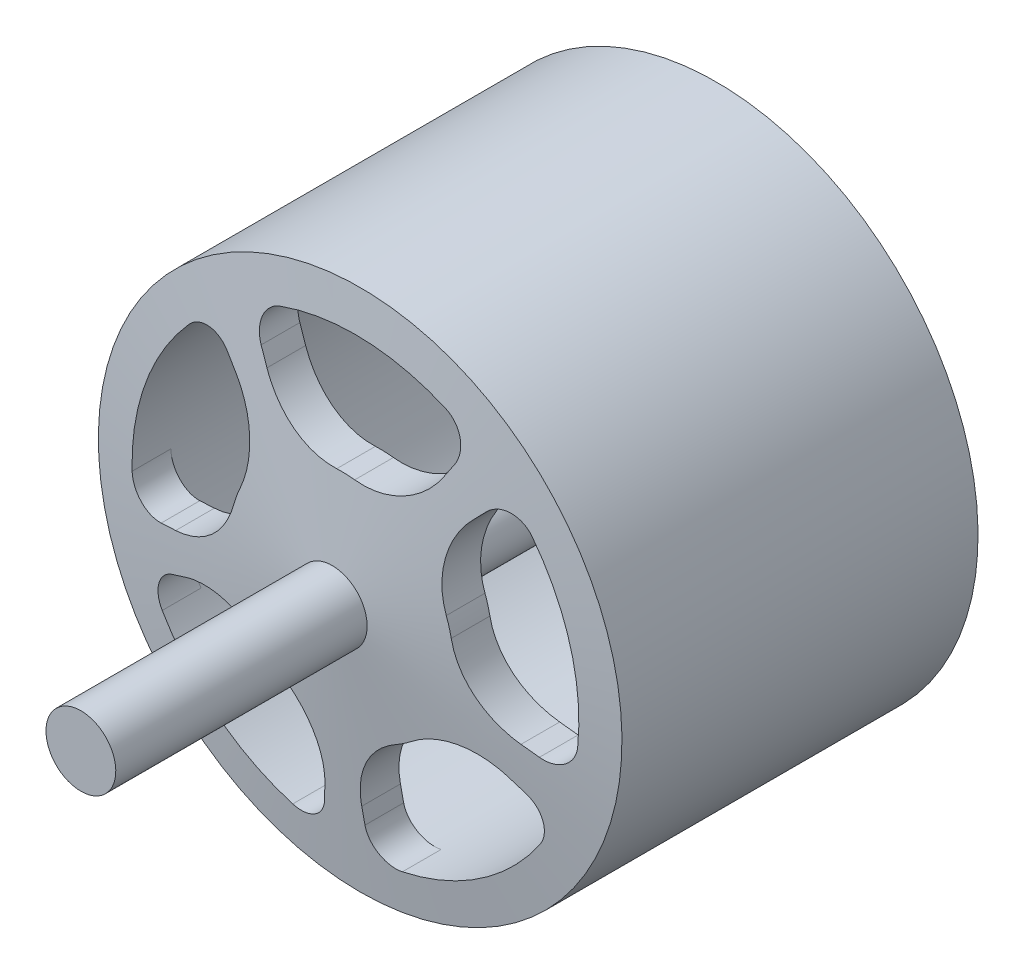
SolidWorks part; units mm, degrees
material "AISI 1020 Steel, Cold Rolled"
ref_plane "Front Plane" through (0, 0, 0) normal (0, 0, 1) x (1, 0, 0)
ref_plane "Top Plane" through (0, 0, 0) normal (0, 1, 0) x (1, 0, 0)
ref_plane "Right Plane" through (0, 0, 0) normal (1, 0, 0) x (0, 0, -1)
sketch "Sketch1" plane through (0, 0, 0) normal (1, 0, 0) x (0, 0, -1)
  line L0 (0, 0) -> (-45.5, 0) construction
  line L1 (-45.5, 0) -> (-45.5, 2.5)
  line L2 (-45.5, 2.5) -> (-27.5, 2.5)
  line L3 (-27.5, 2.5) -> (-25.5, 18.75)
  line L4 (-25.5, 18.75) -> (0, 18.75)
  line L5 (0, 18.75) -> (0, 0) construction
  line L6 (-45.5, 0) -> (0, 0)
  line L8 (-23.0677, 16) -> (0, 16)
  line L9 (0, 16) -> (0, 18.75)
  line L10 (-27.5, 2.5) -> (-24.7706, 2.1641) construction
  line L12 (7.7, 2.5) -> (-24.7292, 2.5)
  line L13 (-23.0677, 16) -> (-24.7706, 2.1641) construction
  line L14 (-23.0677, 16) -> (-24.7292, 2.5)
  line L15 (7.7, 2.5) -> (7.7, 0)
  line L16 (7.7, 0) -> (0, 0)
  dimension "D1" = 18.75
  dimension "D2" = 2.5
  dimension "D3" = 18
  dimension "D4" = 45.5
  dimension "D5" = 20
  dimension "D6" = 16
  dimension "D7" = 53.2
revolve "Revolve1" add sketch "Sketch1" angle 360 about L6
sketch "Sketch2" plane through (0, 0, 0) normal (0, 0, 1) x (1, 0, 0)
  line L0 (0, 0) -> (8.497, 13.5573) construction
  line L1 (0, 0) -> (-7.4924, 14.1373) construction
  line L2 (-6.4886, 12.2433) -> (-5.9233, 11.1765)
  line L3 (7.3587, 11.741) -> (6.7175, 10.718)
  circle A0 centre (0, 0) radius 16 construction
  arc A1 (-5.396, 15.0627) -> (6.4731, 14.6321) centre (0, 0) cw
  circle A2 centre (0, 0) radius 8 construction
  arc A3 (-0.3553, 7.9921) -> (0.9334, 7.9454) centre (0, 0) cw
  arc A4 (6.4731, 14.6321) -> (7.3587, 11.741) centre (5.664, 12.8031) cw
  arc A5 (-6.4886, 12.2433) -> (-5.396, 15.0627) centre (-4.7215, 13.1798) cw
  arc A6 (0.9334, 7.9454) -> (6.7175, 10.718) centre (1.6335, 13.9044) ccw
  arc A7 (-0.3553, 7.9921) -> (-5.9233, 11.1765) centre (-0.6218, 13.9862) cw
  point P18 (4.2485, 6.7786)
  point P21 (-3.7462, 7.0687)
  dimension "D1" = 32
  dimension "D3" = 16
  dimension "D4" = 2
  dimension "D5" = 6
  dimension "D2" = 60
extrude "Cut-Extrude1" cut sketch "Sketch2" along normal through all contours A3 A6 L3 A4 A1 A5 L2 A7
pattern_circular "CirPattern1" count 5 over 360 about axis through (0, 0, 0) along (0, 0, 1) of "Cut-Extrude1"
move or copy body "Body-Move/Copy1" [suppressed] bodies to move or copy 103 parameters "D1"=0, "D2"=0, "D3"=0
